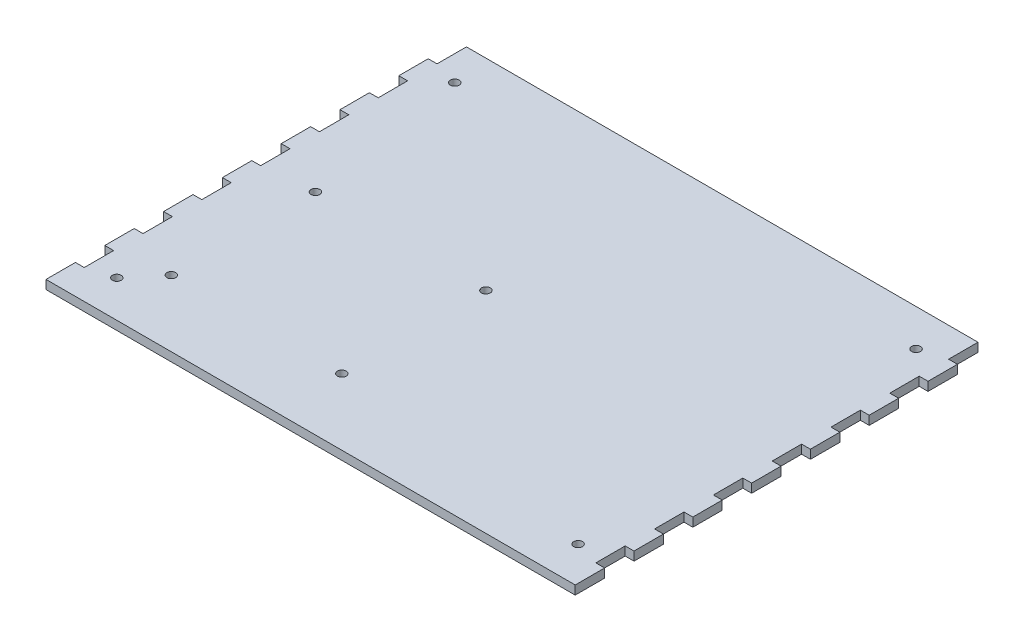
SolidWorks part; units mm, degrees
ref_plane "Plan de face" through (0, 0, 0) normal (0, 0, 1) x (1, 0, 0)
ref_plane "Plan de dessus" through (0, 0, 0) normal (0, 1, 0) x (1, 0, 0)
ref_plane "Plan de droite" through (0, 0, 0) normal (1, 0, 0) x (0, 0, -1)
sketch "Esquisse1" plane through (0, 0, 0) normal (0, 1, 0) x (1, 0, 0)
  line L0 (-78.45, 57.48) -> (78.45, -57.48) construction
  line L1 (-78.45, 57.48) -> (78.45, 57.48) construction
  line L2 (-78.45, 57.48) -> (-78.45, -57.48) construction
  line L3 (-78.45, -57.48) -> (78.45, -57.48) construction
  line L4 (78.45, 57.48) -> (78.45, -57.48) construction
  line L5 (-69.95, 1.5763) -> (-11.95, 1.5763) construction
  line L6 (-73.45, 5.0763) -> (11.55, 5.0763) construction
  line L7 (-73.45, 5.0763) -> (-73.45, -50.9237) construction
  line L8 (-73.45, -50.9237) -> (11.55, -50.9237) construction
  line L9 (11.55, 5.0763) -> (11.55, -50.9237) construction
  line L10 (-69.95, 1.5763) -> (-69.95, -47.4237) construction
  line L11 (-69.95, -47.4237) -> (-11.95, -47.4237) construction
  line L12 (90, 70) -> (-90, -70) construction
  line L13 (-90, 70) -> (90, 70)
  line L14 (-90, 70) -> (-90, -70)
  line L15 (-90, -70) -> (90, -70)
  line L16 (90, 70) -> (90, -70)
  circle A0 centre (-78.45, 57.48) radius 1.5
  circle A1 centre (78.45, 57.48) radius 1.5
  circle A2 centre (78.45, -57.48) radius 1.5
  circle A3 centre (-78.45, -57.48) radius 1.5
  circle A4 centre (-69.95, 1.5763) radius 1.5
  circle A5 centre (-11.95, 1.5763) radius 1.5
  circle A6 centre (-69.95, -47.4237) radius 1.5
  circle A7 centre (-11.95, -47.4237) radius 1.5
  point P4 (0, 0)
  point P26 (0, 0)
  dimension "D3" = 3
  dimension "D4" = 3
  dimension "D1" = 156.9
  dimension "D2" = 114.96
  dimension "D5" = 3.5
  dimension "D6" = 3.5
  dimension "D7" = 56
  dimension "D8" = 85
  dimension "D9" = 58
  dimension "D10" = 49
  dimension "D11" = 6.5563
  dimension "D12" = 5
  dimension "D13" = 140
  dimension "D14" = 180
extrude "Boss.-Extru.1" add sketch "Esquisse1" along normal blind 3
sketch "Esquisse2" plane through (0, 3, 0) normal (0, 1, 0) x (1, 0, 0)
  line L0 (-90, 50) -> (-90, 40)
  line L1 (-90, 70) -> (-87, 70)
  line L2 (-90, 70) -> (-90, 60)
  line L3 (-90, 60) -> (-87, 60)
  line L4 (-87, 70) -> (-87, 60)
  line L5 (-90, 50) -> (-87, 50)
  line L6 (-87, 50) -> (-87, 40)
  line L7 (-90, 40) -> (-87, 40)
  line L8 (-90, 30) -> (-90, 20)
  line L9 (-90, 30) -> (-87, 30)
  line L10 (-87, 30) -> (-87, 20)
  line L11 (-90, 20) -> (-87, 20)
  line L12 (-90, 10) -> (-90, 0)
  line L13 (-90, 10) -> (-87, 10)
  line L14 (-87, 10) -> (-87, 0)
  line L15 (-90, 0) -> (-87, 0)
  line L16 (-90, -10) -> (-90, -20)
  line L17 (-90, -10) -> (-87, -10)
  line L18 (-87, -10) -> (-87, -20)
  line L19 (-90, -20) -> (-87, -20)
  line L20 (-90, -30) -> (-90, -40)
  line L21 (-90, -30) -> (-87, -30)
  line L22 (-87, -30) -> (-87, -40)
  line L23 (-90, -40) -> (-87, -40)
  line L24 (-90, -50) -> (-90, -60)
  line L25 (-90, -50) -> (-87, -50)
  line L26 (-87, -50) -> (-87, -60)
  line L27 (-90, -60) -> (-87, -60)
  line L28 (0, -1.65) -> (0, 1.65) construction
  line L29 (90, -50) -> (87, -50)
  line L30 (87, -50) -> (87, -60)
  line L31 (90, -60) -> (87, -60)
  line L32 (90, -50) -> (90, -60)
  line L33 (90, -30) -> (87, -30)
  line L34 (87, -30) -> (87, -40)
  line L35 (90, -40) -> (87, -40)
  line L36 (90, -30) -> (90, -40)
  line L37 (90, -10) -> (87, -10)
  line L38 (87, -10) -> (87, -20)
  line L39 (90, -20) -> (87, -20)
  line L40 (90, -10) -> (90, -20)
  line L41 (90, 10) -> (87, 10)
  line L42 (87, 10) -> (87, 0)
  line L43 (90, 0) -> (87, 0)
  line L44 (90, 10) -> (90, 0)
  line L45 (90, 30) -> (87, 30)
  line L46 (87, 30) -> (87, 20)
  line L47 (90, 20) -> (87, 20)
  line L48 (90, 30) -> (90, 20)
  line L49 (90, 50) -> (87, 50)
  line L50 (87, 50) -> (87, 40)
  line L51 (90, 40) -> (87, 40)
  line L52 (90, 50) -> (90, 40)
  line L53 (90, 60) -> (87, 60)
  line L54 (87, 70) -> (87, 60)
  line L55 (90, 70) -> (87, 70)
  line L56 (90, 70) -> (90, 60)
  dimension "D1" = 10
  dimension "D2" = 3
  dimension "D3" = 7
extrude "Enlèv. mat.-Extru.1" cut sketch "Esquisse2" against normal up to next
